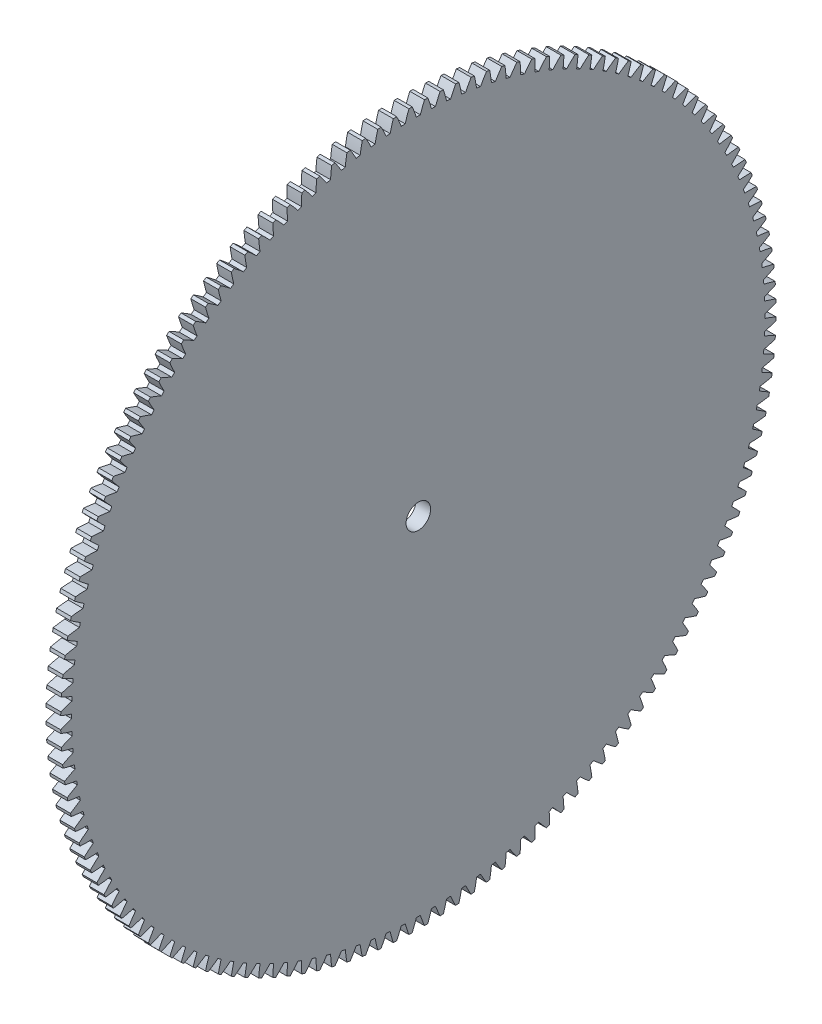
SolidWorks part; units mm, degrees
ref_plane "Plane1" through (0, 0, 0) normal (0, 0, 1) x (1, 0, 0)
ref_plane "Plane2" through (0, 0, 0) normal (0, 1, 0) x (1, 0, 0)
ref_plane "Plane3" through (0, 0, 0) normal (1, 0, 0) x (0, 0, -1)
sketch "HoldingSke" plane through (0, 0, 0) normal (0, 1, 0) x (1, 0, 0)
  line L0 (0, 0) -> (-0.809, -0.5878)
  line L1 (-15, 0) -> (100, 0) construction
  line L2 (0, 0) -> (-2.1039, 2.3779)
  line L3 (0, 0) -> (-11.863, 4.5341)
  line L4 (0, 0) -> (-6.9867, 5.0761)
  line L5 (0, 0) -> (-46.8476, -17.4728)
  line L6 (0, 0) -> (-2.4869, -1.6779)
  line L7 (-2.1039, 2.3779) -> (8.6586, 51.2059)
  line L8 (-76.2, 54.61) -> (-75.3, 54.61)
  line L9 (-71.009, 38.7566) -> (-53.1078, 45.2721)
  line L10 (-76.2, 71.12) -> (104.1128, 71.12)
  line L11 (0, 0) -> (-3, 0)
  line L12 (-76.2, 101.6) -> (-76.162, 101.6)
  line L13 (24.9733, 27.94) -> (52.9518, 28.4284)
  line L14 (24.9733, 27.94) -> (24.9743, 27.94)
  line L15 (24.9733, 27.94) -> (100.4006, 29.5858)
  line L16 (-63.627, -1) -> (-12.827, -1)
  circle A0 centre (0, 0) radius 2.5
  circle A1 centre (0, 0) radius 37.5
  circle A2 centre (0, 0) radius 37.5
  circle A3 centre (0, 0) radius 2.5
  dimension "MHD" = 75
  dimension "Hub_dia" = 75
  dimension "Bore" = 5
  dimension "MBD" = 5
  dimension "Num_teeth" = 144
  dimension "Pitch_radius" = 180.3128
  dimension "Pitch" = 1
  dimension "Width" = 3
  dimension "Overall_len" = 50
  dimension "Show_teeth" = 144
  dimension "Thickness" = 3
  dimension "OAL" = 50.0001
  dimension "T_dim" = 0.9
  dimension "Ap" = 20
  dimension "H" = 19.05
  dimension "Backlash" = 0.038
  dimension "Addendum_fac" = 1
  dimension "Dedendum_fac" = 1.25
  dimension "Clearance_fac" = 0.25
  dimension "Dedendum_add" = 0.001
  dimension "Module" = 1
sketch "BasProSke" plane through (0, 0, 0) normal (0, 1, 0) x (1, 0, 0)
  line L0 (-10, 0) -> (60, 0) construction
  line L1 (0, 0) -> (0, 73)
  line L2 (0, 0) -> (3, 0)
  line L3 (3, 0) -> (3, 73)
  line L4 (3, 73) -> (0, 73)
  dimension "Diameter" = 146
  dimension "Thickness" = 3
revolve "Base-Revolve" add sketch "BasProSke" angle 360 about L0
sketch "TooCutSke" plane through (0, 0, 0) normal (1, 0, 0) x (0, 0, -1)
  line L1 (0, 0) -> (0, 107) construction
  line L2 (0, 0) -> (-0.8519, 71.995) construction
  line L3 (0, 0) -> (-3.1412, 143.9586) construction
  line L4 (-0.8519, 71.995) -> (-1.5706, 71.9793) construction
  arc A0 (0.4074, 70.7478) -> (-0.4074, 70.7478) centre (0, 0) ccw
  arc A1 (1.2644, 73.0145) -> (-1.2644, 73.0145) centre (0, 0) ccw
  circle A2 centre (0, 0) radius 72 construction
  circle A3 centre (0, 0) radius 67.6579 construction
  arc A4 (-0.4074, 70.7478) -> (-1.2644, 73.0145) centre (-27.7508, 61.7048) ccw
  arc A5 (1.2644, 73.0145) -> (0.4074, 70.7478) centre (27.7508, 61.7048) ccw
  dimension "Root_dia" = 141.498
  dimension "Overcut_dia" = 146.0508
  dimension "Pitch_dia" = 144
  dimension "Base_dia" = 135.3157
  dimension "Flank_rad" = 28.8
  dimension "Half_ang" = 1.25
  dimension "Half_CT" = 0.7189
extrude "ToothCut" cut sketch "TooCutSke" along normal through all
fillet "Breaks" [suppressed] radius 0.02
fillet "RootFillets" [suppressed] radius 0.251
pattern_circular "TeethCuts" count 144 every 2.5 about axis through (-10, 0, 0) along (1, 0, 0) of "ToothCut", "RootFillets", "Breaks"
sketch "HubNeaOneSke" plane through (0, 0, 0) normal (-1, 0, 0) x (0, 0, 1)
  circle A0 centre (0, 0) radius 37.5
  dimension "Diameter" = 75
extrude "HubNearOne" [suppressed] add sketch "HubNeaOneSke" along normal blind 47.0001
sketch "HubNeaBotSke" plane through (0, 0, 0) normal (-1, 0, 0) x (0, 0, 1)
  circle A0 centre (0, 0) radius 37.5
  dimension "Diameter" = 75
extrude "HubNearBoth" [suppressed] add sketch "HubNeaBotSke" along normal blind 23.5
ref_plane "FarPln" through (3, 0, 0) normal (1, 0, 0) x (0, 0, -1)
sketch "HubFarSke" plane through (3, 0, 0) normal (1, 0, 0) x (0, 0, -1)
  circle A0 centre (0, 0) radius 37.5
  dimension "Diameter" = 75
extrude "HubFar" [suppressed] add sketch "HubFarSke" along normal blind 23.5
sketch "BorSke" plane through (0, 0, 0) normal (1, 0, 0) x (0, 0, -1)
  circle A0 centre (0, 0) radius 2.5
  dimension "Diameter" = 5
extrude "Bore" cut sketch "BorSke" along normal mid plane 100.0001
sketch "KeySke" plane through (0, 0, 0) normal (1, 0, 0) x (0, 0, -1)
  line L0 (-1, 0) -> (-1, 3.4)
  line L1 (-1, 3.4) -> (1, 3.4)
  line L2 (1, 3.4) -> (1, 0)
  line L3 (0, 0) -> (0, 34) construction
  line L4 (-1, 0) -> (1, 0)
  dimension "Offset" = 3.4
  dimension "Width" = 2
extrude "Keyway" [suppressed] cut sketch "KeySke" along normal mid plane 100.0001
pattern_circular "Keyway2" [suppressed] count 2 every 90 about axis through (-10, 0, 0) along (1, 0, 0)
equation "' \"Module@HoldingSke\" = 6.35"
equation "' \"Num_teeth@HoldingSke\" = 12"
equation "' \"Ap@HoldingSke\" =  20"
equation "' \"Width@HoldingSke\" = 0.5 * 25.4"
equation "' \"Hub_dia@HoldingSke\"= 1 * 25.4"
equation "' \"Overall_len@HoldingSke\" = 1.0 * 25.4"
equation "' \"Bore@HoldingSke\" = 0.75 * 25.4"
equation "' \"T_dim@HoldingSke\" = 0.1 * 25.4"
equation "' \"Width@KeySke\" = 0.25 * 25.4"
equation "' \"Show_teeth@HoldingSke\" = 13"
equation "' \"Backlash@HoldingSke\" = 0.009 * 25.4"
equation "' \"Addendum_fac@HoldingSke\" = 1.0"
equation "' \"Dedendum_fac@HoldingSke\" = 1.25"
equation "' \"Dedendum_add@HoldingSke\" = 0.00005 * 25.4"
equation "' \"Clearance_fac@HoldingSke\" = 0.25"
equation "\"Pitch@HoldingSke\" = 1 / \"Module@HoldingSke\""
equation "\"Overcut_dia@TooCutSke\" = (\"Num_teeth@HoldingSke\" + 2 * \"Addendum_fac@HoldingSke\") / \"Pitch@HoldingSke\" + 0.002 * 25.4"
equation "\"Pitch_dia@TooCutSke\" = \"Num_teeth@HoldingSke\" / \"Pitch@HoldingSke\""
equation "\"Base_dia@TooCutSke\" = \"Num_teeth@HoldingSke\" / \"Pitch@HoldingSke\" * cos((\"Ap@HoldingSke\"  * 3.14159265 / 180))"
equation "\"Root_dia@TooCutSke\" = (\"Num_teeth@HoldingSke\" + 2) / \"Pitch@HoldingSke\" - 2 * (\"Addendum_fac@HoldingSke\" + \"Dedendum_fac@HoldingSke\") / \"Pitch@HoldingSke\" - \"Dedendum_add@HoldingSke\" * 2"
equation "\"Half_ang@TooCutSke\" = 180 / \"Num_teeth@HoldingSke\""
equation "\"Half_CT@TooCutSke\" = \"Num_teeth@HoldingSke\" / \"Pitch@HoldingSke\" * sin((3.14159265 / 2 / \"Num_teeth@HoldingSke\")) / 2 - 7 * \"Backlash@HoldingSke\" / 4"
equation "\"Flank_rad@TooCutSke\" = \"Num_teeth@HoldingSke\" / \"Pitch@HoldingSke\" / 5"
equation "\"Radius@RootFillets\" = \"Clearance_fac@HoldingSke\" / \"Pitch@HoldingSke\" + \"Dedendum_add@HoldingSke\""
equation "\"Break_rad@Breaks\" = 0.02 / \"Pitch@HoldingSke\""
equation "\"Thickness@HoldingSke\" = \"Width@HoldingSke\""
equation "\"OAL@HoldingSke\" = \"Thickness@HoldingSke\""
equation "\"MHD@HoldingSke\" = (\"Num_teeth@HoldingSke\" + 2) / \"Pitch@HoldingSke\" - 2 * (\"Addendum_fac@HoldingSke\" + \"Dedendum_fac@HoldingSke\")  / \"Pitch@HoldingSke\" - \"Dedendum_add@HoldingSke\" * 2"
equation "\"MBD@HoldingSke\" = (\"Num_teeth@HoldingSke\" + 2) / \"Pitch@HoldingSke\" - 2 * (\"Addendum_fac@HoldingSke\" + \"Dedendum_fac@HoldingSke\")  / \"Pitch@HoldingSke\" - \"Dedendum_add@HoldingSke\" * 2 - 0.002 * 25.4"
equation "\"MHD@HoldingSke\" = ((sgn( \"MHD@HoldingSke\" - \"Hub_dia@HoldingSke\" )-1)*( \"MHD@HoldingSke\" - \"Hub_dia@HoldingSke\" ))/-2+ \"Hub_dia@HoldingSke\""
equation "\"MBD@HoldingSke\" = ((sgn( \"MBD@HoldingSke\" - \"Bore@HoldingSke\" )-1)*( \"MBD@HoldingSke\" - \"Bore@HoldingSke\" ))/-2+ \"Bore@HoldingSke\""
equation "\"OAL@HoldingSke\" = ((sgn( \"OAL@HoldingSke\" - \"Overall_len@HoldingSke\" )+1)*( \"OAL@HoldingSke\" - \"Overall_len@HoldingSke\" ))/2 + \"Overall_len@HoldingSke\" + 0.000002 * 25.4"
equation "\"Num_teeth@TeethCuts\" = int( \"Show_teeth@HoldingSke\" ) + 1"
equation "\"Num_teeth@TeethCuts\" = ((sgn( \"Num_teeth@TeethCuts\" - \"Num_teeth@HoldingSke\" )-1)*( \"Num_teeth@TeethCuts\" - \"Num_teeth@HoldingSke\" ))/-2+ \"Num_teeth@HoldingSke\""
equation "\"Num_teeth@TeethCuts\" = ((sgn( \"Num_teeth@TeethCuts\" - 2.0)+1)*( \"Num_teeth@TeethCuts\" - 2.0))/2 +2.0"
equation "\"Angle@TeethCuts\" = 360.0 / \"Num_teeth@HoldingSke\""
equation "\"Diameter@BasProSke\" = (\"Num_teeth@HoldingSke\" + 2 * \"Addendum_fac@HoldingSke\") / \"Pitch@HoldingSke\""
equation "\"Thickness@BasProSke\"  = \"Thickness@HoldingSke\""
equation "' \"Fillet_rad@BasProSke\" =  \"Thickness@HoldingSke\" * 0.05"
equation "\"MHD@HoldingSke\" = ((sgn( \"MHD@HoldingSke\" - \"Root_dia@TooCutSke\" )-1)*( \"MHD@HoldingSke\" - \"Root_dia@TooCutSke\" ))/-2+ \"Root_dia@TooCutSke\""
equation "\"Diameter@HubNeaOneSke\" = \"MHD@HoldingSke\""
equation "\"Length@HubNearOne\" = \"OAL@HoldingSke\" - \"Thickness@BasProSke\""
equation "\"Diameter@HubNeaBotSke\" = \"MHD@HoldingSke\""
equation "\"Length@HubNearBoth\" = ( \"OAL@HoldingSke\" - \"Thickness@BasProSke\" ) / 2.0"
equation "\"Thickness@FarPln\" = \"Thickness@BasProSke\""
equation "\"Diameter@HubFarSke\" = \"MHD@HoldingSke\""
equation "\"Length@HubFar\" = ( \"OAL@HoldingSke\" - \"Thickness@BasProSke\" ) / 2.0"
equation "\"Diameter@BorSke\" = \"MBD@HoldingSke\""
equation "\"D1@Bore\" = \"OAL@HoldingSke\" * 2.0"
equation "\"D1@Keyway\" = \"OAL@HoldingSke\" * 2.0"
equation "\"Offset@KeySke\" = \"T_dim@HoldingSke\" + \"MBD@HoldingSke\" / 2.0"
